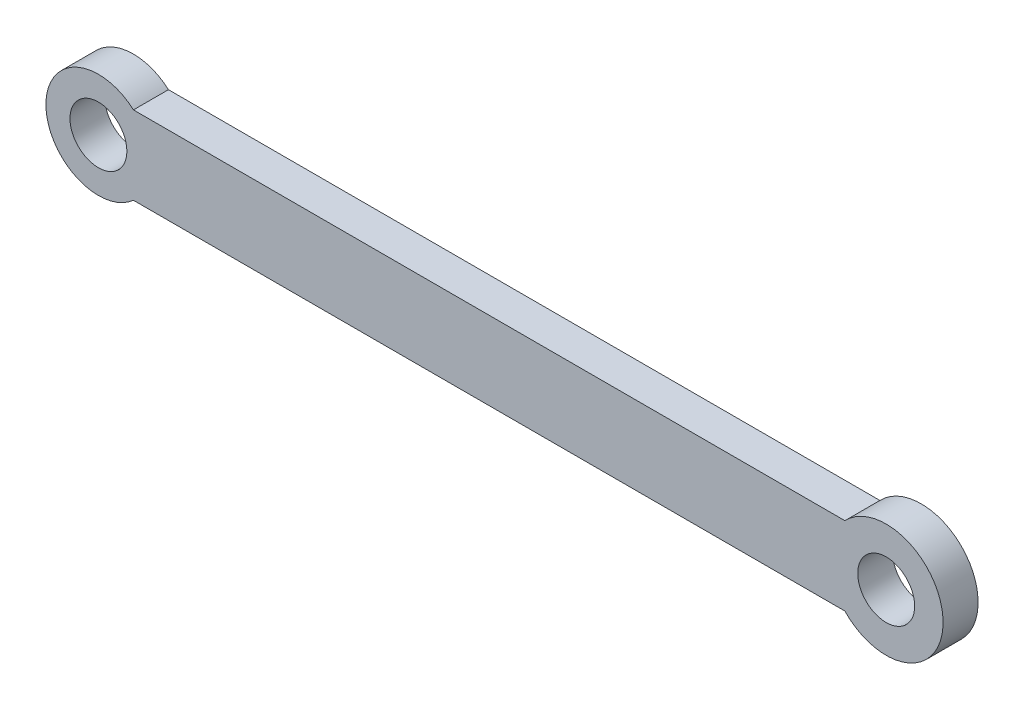
SolidWorks part; units mm, degrees
ref_plane "Front Plane" through (0, 0, 0) normal (0, 0, 1) x (1, 0, 0)
ref_plane "Top Plane" through (0, 0, 0) normal (0, 1, 0) x (1, 0, 0)
ref_plane "Right Plane" through (0, 0, 0) normal (1, 0, 0) x (0, 0, -1)
sketch "Sketch1" plane through (0, 0, 0) normal (0, 0, 1) x (1, 0, 0)
  line L1 (4, 4.4721) -> (90, 4.4721)
  line L2 (4, 4.4721) -> (4, -4.4721)
  line L3 (4, -4.4721) -> (90, -4.4721)
  line L4 (90, 4.4721) -> (90, -4.4721)
  circle A0 centre (0, 0) radius 3.25
  circle A1 centre (0, 0) radius 6
  dimension "D1" = 6.5
  dimension "D2" = 12
  dimension "D3" = 4
  dimension "D4" = 90
extrude "Boss-Extrude2" add sketch "Sketch1" along normal blind 4 contours L2 A1 A0 | L2 A1 | A1 L3 L4 L1
sketch "Sketch2" plane through (0, 0, 4) normal (0, 0, 1) x (1, 0, 0)
  line L0 (90, 4.4721) -> (90, -4.4721) construction
  circle A0 centre (90, 0) radius 6.5
  circle A1 centre (90, 0) radius 3.25
  dimension "D1" = 6.5
  dimension "D2" = 13
extrude "Boss-Extrude3" add sketch "Sketch2" against normal up to surface (4 mm away) up to face at (3.25, 0, 0)
sketch "Sketch3" plane through (0, 0, 4) normal (0, 0, 1) x (1, 0, 0)
  line L0 (90, 3.25) -> (90, -3.25) construction
  circle A0 centre (90, 0) radius 3.25
  dimension "D1" = 6.5
extrude "Cut-Extrude1" cut sketch "Sketch3" against normal blind 10
